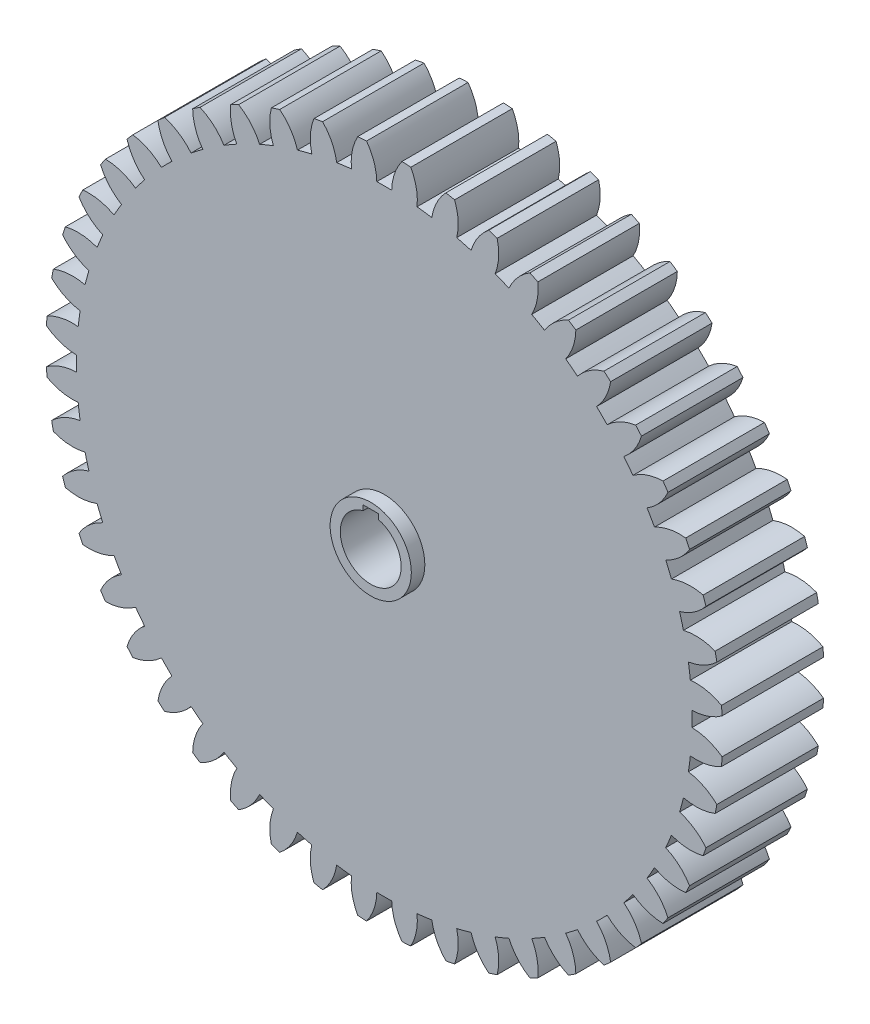
SolidWorks part; units mm, degrees
material "Plain Carbon Steel"
ref_plane "Front Plane" through (0, 0, 0) normal (0, 0, 1) x (1, 0, 0)
ref_plane "Top Plane" through (0, 0, 0) normal (0, 1, 0) x (1, 0, 0)
ref_plane "Right Plane" through (0, 0, 0) normal (1, 0, 0) x (0, 0, -1)
sketch "Sketch2" plane through (0, 0, 0) normal (0, 0, 1) x (1, 0, 0)
  circle A0 centre (0, 0) radius 50
  circle A1 centre (0, 0) radius 48 construction
  dimension "D1" = 96
  dimension "D2" = 100
extrude "Boss-Extrude1" add sketch "Sketch2" along normal mid plane 15
sketch "Sketch3" plane through (0, 0, 0) normal (0, 0, 1) x (1, 0, 0)
  line L0 (0, 50) -> (0, 0) construction
  line L1 (0, 0) -> (6.5263, 49.5722) construction
  line L2 (0, 0) -> (3.2702, 49.8929) construction
  line L3 (-1.1008, 45.4867) -> (0, 0) construction
  line L4 (-2.2887, 49.9476) -> (0, 43.6593) construction
  line L5 (-1.5705, 47.9743) -> (1.5705, 47.9743) construction
  line L6 (1.5705, 47.9743) -> (4.7048, 47.7689) construction
  circle A0 centre (0, 0) radius 46 construction
  circle A2 centre (0, 0) radius 50 construction
  arc A3 (-2.6178, 49.9314) -> (-1.1008, 45.4867) centre (-8.9254, 45.2973) cw
  arc A4 (2.6178, 49.9314) -> (1.1008, 45.4867) centre (8.9254, 45.2973) ccw
  circle A5 centre (0, 0) radius 48 construction
  arc A6 (1.1008, 45.4867) -> (-1.1008, 45.4867) centre (0, 0) ccw
  circle A7 centre (0, 0) radius 50
  arc A8 (2.6178, 49.9314) -> (-2.6178, 49.9314) centre (0, 0) ccw
  dimension "D1" = 7.5
  dimension "D2" = 4
  dimension "D4" = 20
  dimension "D3" = 0.5
  dimension "D5" = 0
extrude "Cut-Extrude1" cut sketch "Sketch3" against normal through all both and the other way through all
sketch "Sketch4" plane through (0, 0, 7.5) normal (0, 0, 1) x (1, 0, 0)
  line L1 (-1.125, 3.6071) -> (1.125, 3.6071)
  line L2 (-1.125, 3.6071) -> (-1.125, 5.1071)
  line L3 (-1.125, 5.1071) -> (1.125, 5.1071)
  line L4 (1.125, 3.6071) -> (1.125, 5.1071)
  arc A0 (-1.125, 4.3571) -> (1.125, 4.3571) centre (0, 0) ccw
  circle A1 centre (0, 0) radius 6
  point P8 (0, 3.6071)
  point P9 (-1.125, 4.3571)
  dimension "D1" = 12
  dimension "D2" = 9
  dimension "D3" = 2.25
  dimension "D4" = 1.5
extrude "Boss-Extrude2" add sketch "Sketch4" along normal blind 2 contours A1 A0 L2 L3 L4
mirror "Mirror1" about plane through (0, 0, 0) normal (0, 0, 1) of "Boss-Extrude2"
sketch "Sketch5" plane through (0, 0, 7.5) normal (0, 0, 1) x (1, 0, 0)
  line L3 (1.125, 4.3571) -> (1.125, 5.1071)
  line L4 (1.125, 4.3571) -> (1.125, 5.1071)
  line L5 (1.125, 5.1071) -> (-1.125, 5.1071)
  line L6 (1.125, 5.1071) -> (-1.125, 5.1071)
  line L7 (-1.125, 5.1071) -> (-1.125, 4.3571)
  line L8 (-1.125, 5.1071) -> (-1.125, 4.3571)
  arc A1 (-1.125, 4.3571) -> (1.125, 4.3571) centre (0, 0) ccw
  arc A2 (-1.125, 4.3571) -> (1.125, 4.3571) centre (0, 0) ccw
  dimension "D1" = 0
extrude "Cut-Extrude7" cut sketch "Sketch5" along normal through all both and the other way through all
pattern_circular "CirPattern1" count 48 over 360 about axis through (0, 0, 0) along (0, 0, 1) of "Cut-Extrude1"
equation "\"module\"= 2mm"
equation "\"pressure angle\"= 20"
equation "\"num of teeth\"= 48"
equation "\"D1@Sketch2\"= \"module\" * \"num of teeth\""
equation "\"D2@Sketch2\"= (\"num of teeth\"+2) * \"module\""
equation "\"D1@Sketch3\"= 360 / \"num of teeth\""
equation "\"D2@Sketch3\"= \"module\" * 2"
equation "\"D4@Sketch3\"= \"pressure angle\""
equation "\"D3@Sketch4\"= 9 / 4"
equation "\"D4@Sketch4\"= 9 / 6"
equation "\"D1@CirPattern1\"= \"num of teeth\""
